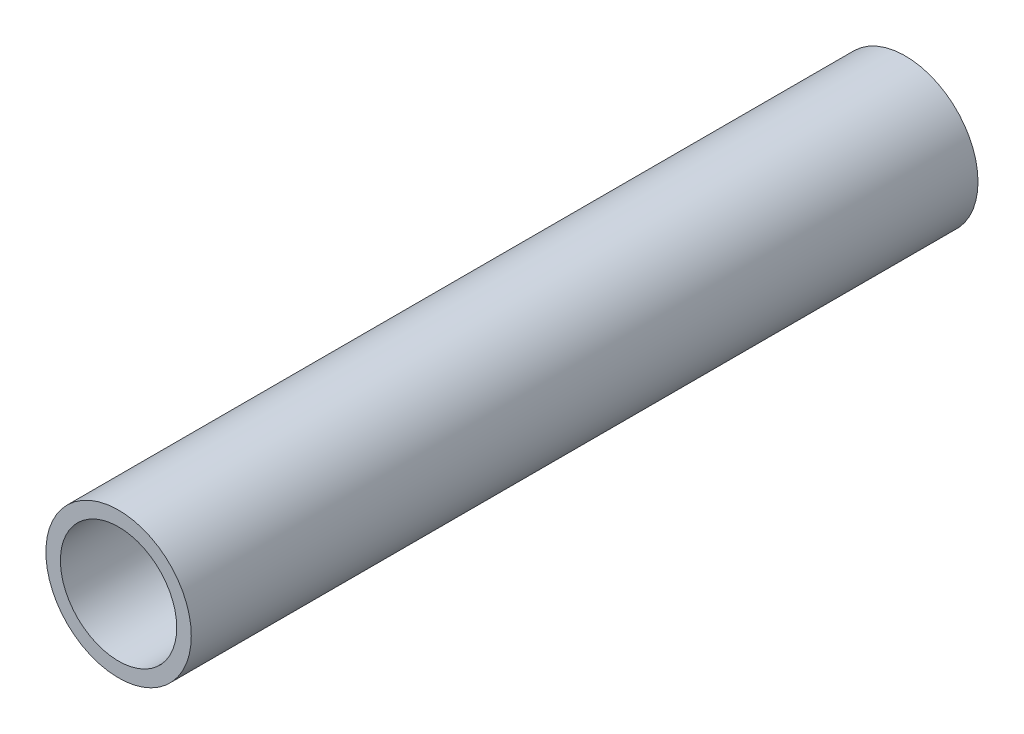
SolidWorks part; units mm, degrees
ref_plane "Front Plane" through (0, 0, 0) normal (0, 0, 1) x (1, 0, 0)
ref_plane "Top Plane" through (0, 0, 0) normal (0, 1, 0) x (1, 0, 0)
ref_plane "Right Plane" through (0, 0, 0) normal (1, 0, 0) x (0, 0, -1)
sketch "Sketch1" plane through (0, 0, 0) normal (0, 0, 1) x (1, 0, 0)
  circle A0 centre (0, 0) radius 1.25
  circle A1 centre (0, 0) radius 1
extrude "Boss-Extrude1" add sketch "Sketch1" along normal blind 13.525
equation "\"D1@Boss-Extrude1\"= \"HL@parametersSketch@prostheticParameters.SLDPRT\" * 0.165 - 3 - 4 - 10'Ring MIP Tube"
